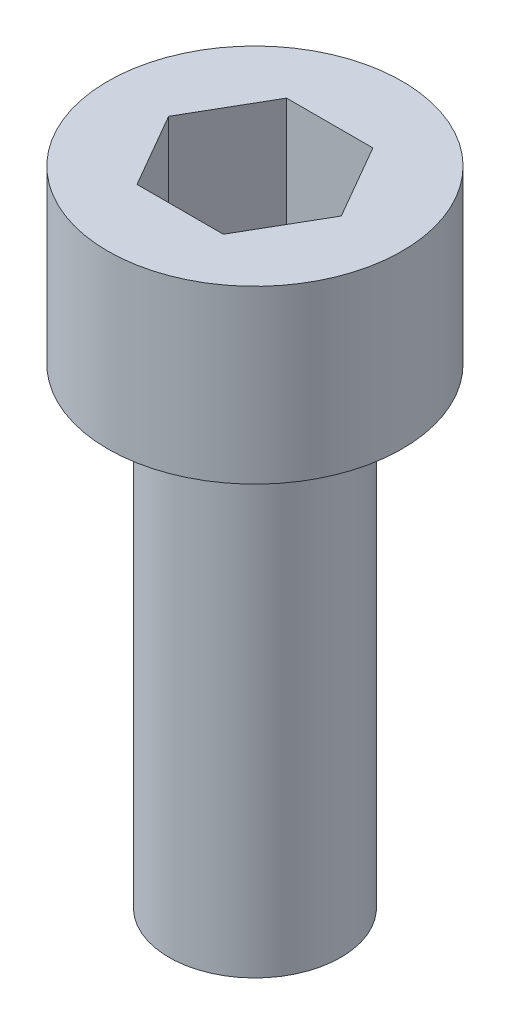
SolidWorks part; units mm, degrees
ref_plane "Front Plane" through (0, 0, 0) normal (0, 0, 1) x (1, 0, 0)
ref_plane "Top Plane" through (0, 0, 0) normal (0, 1, 0) x (1, 0, 0)
ref_plane "Right Plane" through (0, 0, 0) normal (1, 0, 0) x (0, 0, -1)
sketch "Sketch1" plane through (0, 0, 0) normal (0, 1, 0) x (1, 0, 0)
  circle A0 centre (0, 0) radius 5
  dimension "D1" = 10
extrude "Boss-Extrude1" add sketch "Sketch1" along normal blind 5.82
sketch "Sketch2" plane through (0, 0, 0) normal (0, -1, 0) x (1, 0, 0)
  circle A0 centre (0, 0) radius 2.92
  dimension "D1" = 5.84
extrude "Boss-Extrude2" add sketch "Sketch2" along normal blind 16
sketch "Sketch3" plane through (0, 5.82, 0) normal (0, 1, 0) x (1, 0, 0)
  line L7 (2.9329, 0) -> (1.4665, 2.54)
  line L8 (1.4665, 2.54) -> (-1.4665, 2.54)
  line L9 (-1.4665, 2.54) -> (-2.9329, 0)
  line L10 (-2.9329, 0) -> (-1.4665, -2.54)
  line L11 (-1.4665, -2.54) -> (1.4665, -2.54)
  line L12 (1.4665, -2.54) -> (2.9329, 0)
  circle A0 centre (0, 0) radius 2.54 construction
  dimension "D1" = 5.08
extrude "Cut-Extrude1" cut sketch "Sketch3" against normal blind 4.23
